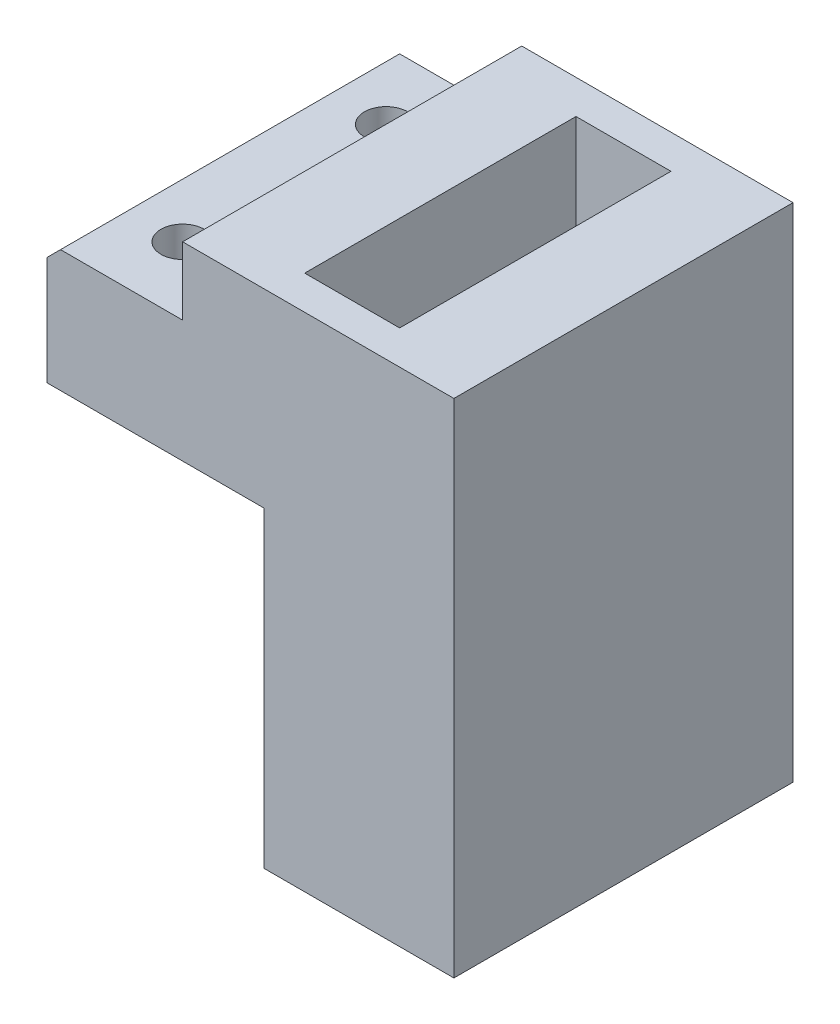
SolidWorks part; units mm, degrees
ref_plane "Front Plane" through (0, 0, 0) normal (0, 0, 1) x (1, 0, 0)
ref_plane "Top Plane" through (0, 0, 0) normal (0, 1, 0) x (1, 0, 0)
ref_plane "Right Plane" through (0, 0, 0) normal (1, 0, 0) x (0, 0, -1)
sketch "Sketch1" plane through (0, 0, 0) normal (0, 1, 0) x (1, 0, 0)
  line L0 (0, -12.5) -> (0, 12.5)
  line L1 (0, 12.5) -> (30, 12.5)
  line L2 (30, 12.5) -> (30, -12.5)
  line L3 (30, -12.5) -> (0, -12.5)
  point P4 (0, 0)
  dimension "D1" = 25
  dimension "D2" = 30
extrude "Boss-Extrude1" add sketch "Sketch1" along normal blind 14
sketch "Sketch2" plane through (0, 14, 0) normal (0, 1, 0) x (1, 0, 0)
  line L0 (0, 0) -> (5, 0)
  line L1 (0, 12.5) -> (0, -12.5) construction
  line L2 (5, 0) -> (5, 7.5)
  line L3 (5, 0) -> (5, -7.5)
  dimension "D1" = 15
  dimension "D2" = 5
hole_wizard "Ø3.2 (3.2) Diameter Hole1" positions "Sketch3" profile "Sketch4" hole size "Ø3.2" standard "ISO" end condition through all
sketch "Sketch3" plane through (0, 14, 0) normal (0, 1, 0) x (1, 0, 0)
  point P0 (5, 7.5)
  point P3 (5, -7.5)
sketch "Sketch4" plane through (5, 14, -7.5) normal (1, 0, 0) x (0, 0, 1)
  line L0 (0, 0) -> (0, 14)
  line L1 (0, 14) -> (1.6, 14)
  line L2 (1.6, 14) -> (1.6, 0)
  line L5 (1.6, 0) -> (0, 0)
  line L11 (0, -6.35) -> (0, 107.95) construction
  dimension "Thru Hole Dia." = 3.2
  dimension "Thru Hole Depth" = 14
sketch "Sketch5" plane through (0, 14, 0) normal (0, 1, 0) x (1, 0, 0)
  line L0 (5, 0) -> (30, 0) construction
  line L1 (30, -12.5) -> (30, 12.5) construction
  line L2 (0, 12.5) -> (0, -12.5) construction
  line L3 (23.5, -10) -> (16.5, -10)
  line L4 (23.5, -10) -> (23.5, 10)
  line L5 (23.5, 10) -> (16.5, 10)
  line L6 (16.5, -10) -> (16.5, 10)
  line L7 (23.5, -10) -> (16.5, 10) construction
  line L8 (23.5, 10) -> (16.5, -10) construction
  point P5 (20, 0)
  dimension "D1" = 7
  dimension "D2" = 20
  dimension "D3" = 20
extrude "Cut-Extrude1" cut sketch "Sketch5" against normal blind 10
sketch "Sketch6" plane through (0, 14, 0) normal (0, 1, 0) x (1, 0, 0)
  line L0 (0, -12.5) -> (30, -12.5) construction
  line L1 (0, 12.5) -> (10, 12.5)
  line L2 (0, 12.5) -> (0, -12.5)
  line L3 (0, -12.5) -> (10, -12.5)
  line L4 (10, 12.5) -> (10, -12.5)
  dimension "D1" = 10
extrude "Cut-Extrude2" cut sketch "Sketch6" against normal blind 5
chamfer "Chamfer1" distance 1 angle 45 1 edges at (0, 9, 0)
sketch "Sketch7" plane through (0, 0, 0) normal (0, -1, 0) x (1, 0, 0)
  line L1 (30, -12.5) -> (16, -12.5)
  line L2 (30, -12.5) -> (30, 12.5)
  line L3 (30, 12.5) -> (16, 12.5)
  line L4 (16, -12.5) -> (16, 12.5)
  line L5 (0, 12.5) -> (30, 12.5) construction
  point P4 (16.1186, 12.5)
  dimension "D1" = 14
extrude "Boss-Extrude2" add sketch "Sketch7" along normal blind 23
